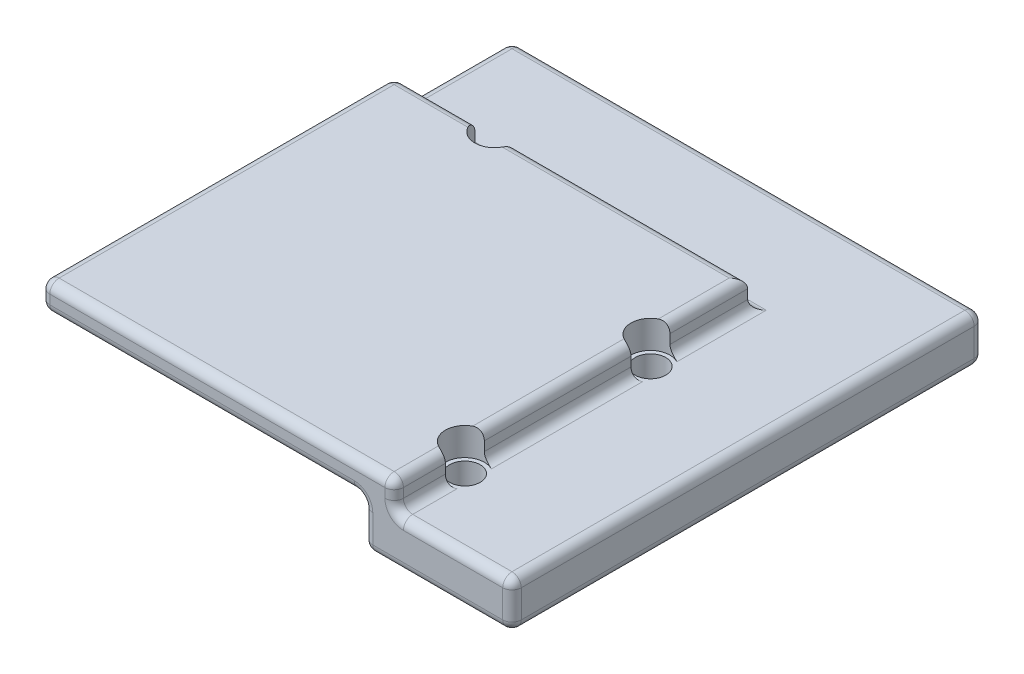
SolidWorks part; units mm, degrees
ref_plane "Front Plane" through (0, 0, 0) normal (0, 0, 1) x (1, 0, 0)
ref_plane "Top Plane" through (0, 0, 0) normal (0, 1, 0) x (1, 0, 0)
ref_plane "Right Plane" through (0, 0, 0) normal (1, 0, 0) x (0, 0, -1)
sketch "Sketch1" plane through (0, 0, 0) normal (0, 0, 1) x (1, 0, 0)
  line L1 (-25.4, -4) -> (25.4, -4)
  line L2 (-25.4, -4) -> (-25.4, 4)
  line L3 (-25.4, 4) -> (25.4, 4)
  line L4 (25.4, -4) -> (25.4, 4)
  line L5 (-25.4, -4) -> (25.4, 4) construction
  line L6 (-25.4, 4) -> (25.4, -4) construction
  point P0 (0, 0)
  dimension "D1" = 50.8
  dimension "D2" = 8
extrude "Boss-Extrude1" add sketch "Sketch1" along normal blind 50.8
sketch "Sketch2" plane through (0, 0, 50.8) normal (0, 0, 1) x (1, 0, 0)
  line L0 (25.4, -4) -> (25.4, 4) construction
  line L1 (-25.4, -4) -> (9.4, -4)
  line L2 (-25.4, -4) -> (-25.4, 1)
  line L3 (-25.4, 1) -> (9.4, 1)
  line L4 (9.4, -4) -> (9.4, 1)
  dimension "D1" = 5
  dimension "D2" = 16
extrude "Cut-Extrude2" cut sketch "Sketch2" against normal offset from surface (34.8 mm away) 16 up to face at (0, 0, 0)
sketch "Sketch3" plane through (0, 4, 0) normal (0, 1, 0) x (1, 0, 0)
  line L0 (-25.4, -12.7) -> (12.7, -12.7)
  line L1 (-25.4, -50.8) -> (-25.4, 0) construction
  line L2 (12.7, -12.7) -> (12.7, -50.8)
  line L3 (25.4, -50.8) -> (-25.4, -50.8) construction
  line L4 (12.7, -50.8) -> (25.4, -50.8)
  line L5 (25.4, -50.8) -> (25.4, 0)
  line L6 (25.4, 0) -> (-25.4, 0)
  line L7 (-25.4, 0) -> (-25.4, -12.7)
  point P4 (-19.05, -7.23)
  dimension "D1" = 12.7
  dimension "D2" = 12.7
extrude "Cut-Extrude3" cut sketch "Sketch3" against normal offset from surface (3 mm away) 5 up to face at (3.1333, -4, 22.2667)
fillet "Fillet1" radius 1 29 edges at (12.7, 2.5, 50.8) (9.4, -1.5, 50.8) (17.4, -4, 50.8) (0, -4, 0) (9.4, -4, 33.4) (25.4, -1.5, 0) (25.4, -4, 25.4) (25.4, -1.5, 50.8) (9.4, -1.5, 16) (-8, -4, 16) (-25.4, 2.5, 50.8) (-25.4, -1.5, 16) (-25.4, -4, 8) (-25.4, -1.5, 0) (-25.4, 2.5, 12.7) (0, 1, 0) (25.4, 1, 25.4) (19.05, 1, 50.8) (12.7, 1, 31.75) (-6.35, 1, 12.7) (-25.4, 1, 6.35) (-25.4, 4, 31.75) (-6.35, 4, 12.7) (12.7, 4, 31.75) (-6.35, 4, 50.8) (-8, 1, 16) (-25.4, 1, 33.4) (-8, 1, 50.8) (9.4, 1, 33.4)
sketch "Sketch4" plane through (0, 1, 0) normal (0, 1, 0) x (1, 0, 0)
  line L0 (-24.4, 0) -> (24.4, 0) construction
  line L1 (25.4, -1) -> (25.4, -49.8) construction
  circle A0 centre (-14.6, -12.7) radius 2.1
  circle A1 centre (12.7, -43.18) radius 2.1
  circle A2 centre (12.7, -23.18) radius 2.1
  dimension "D5" = 4.2
  dimension "D6" = 20
  dimension "D1" = 12.7
  dimension "D2" = 27.3
  dimension "D3" = 12.7
  dimension "D4" = 12.7
  dimension "D7" = 30.48
extrude "Cut-Extrude4" cut sketch "Sketch4" along normal through all
sketch "Sketch5" plane through (0, 1, 0) normal (0, 1, 0) x (1, 0, 0)
  circle A0 centre (-14.6, -12.7) radius 1.65
  circle A1 centre (12.7, -23.18) radius 1.65
  circle A2 centre (12.7, -43.18) radius 1.65
  dimension "D1" = 3.3
extrude "Cut-Extrude5" cut sketch "Sketch5" against normal through all
